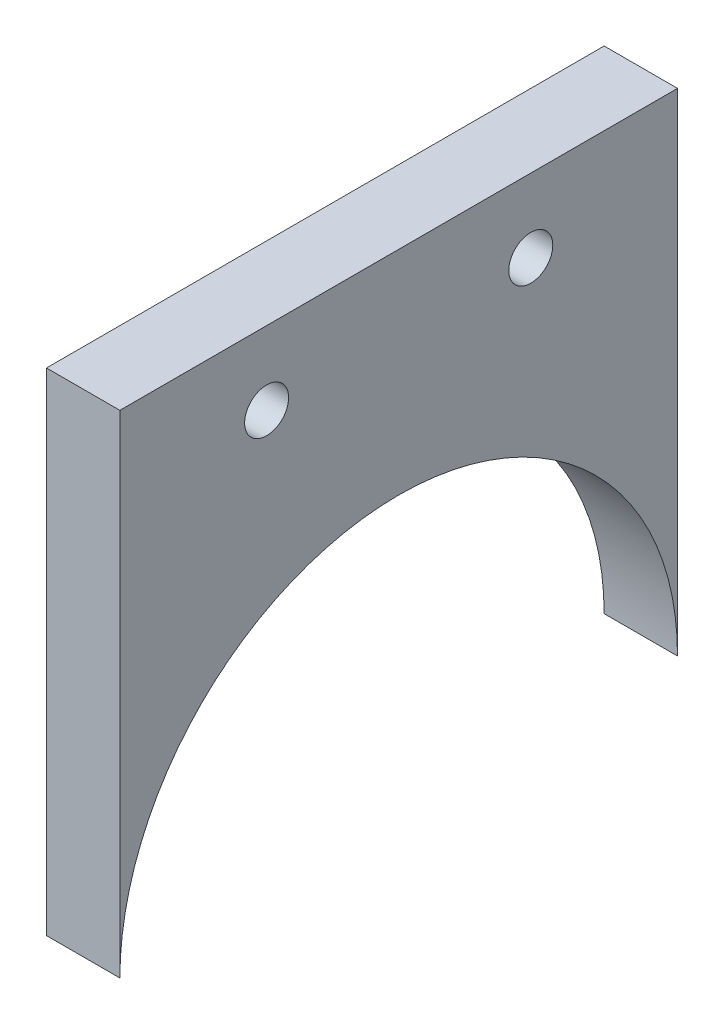
SolidWorks part; units mm, degrees
material "PMMA"
ref_plane "Front Plane" through (0, 0, 0) normal (0, 0, 1) x (1, 0, 0)
ref_plane "Top Plane" through (0, 0, 0) normal (0, 1, 0) x (1, 0, 0)
ref_plane "Right Plane" through (0, 0, 0) normal (1, 0, 0) x (0, 0, -1)
sketch "Schizzo1" plane through (0, 0, 0) normal (1, 0, 0) x (0, 0, -1)
  line L0 (19, 16.75) -> (-19, -16.75) construction
  line L1 (-19, 16.75) -> (19, 16.75)
  line L2 (-19, 16.75) -> (-19, -16.75)
  line L3 (-19, -16.75) -> (19, -16.75)
  line L4 (19, 16.75) -> (19, -16.75)
  point P4 (0, 0)
  dimension "D1" = 38
  dimension "D2" = 33.5
extrude "Estrusione-Estrusione1" add sketch "Schizzo1" along normal blind 5
sketch "Schizzo2" plane through (0, 0, 0) normal (1, 0, 0) x (0, 0, -1)
  line L0 (-19, -16.75) -> (19, -16.75) construction
  line L1 (-19, 16.75) -> (-19, -16.75) construction
  line L2 (19, 16.75) -> (-19, 16.75) construction
  line L3 (19, -16.75) -> (19, 16.75) construction
  line L4 (0, 16.75) -> (0, 2.25) construction
  circle A0 centre (0, -16.75) radius 19
  circle A1 centre (-9, 11.75) radius 1.5
  circle A2 centre (9, 11.75) radius 1.5
  dimension "D1" = 3
  dimension "D2" = 10
  dimension "D3" = 5
  dimension "D4" = 9
  dimension "D5" = 10
extrude "Taglio-Estrusione1" cut sketch "Schizzo2" along direction (1, 0, 0) on the side of the normal through all
equation "\"Thickness\"=5"
equation "\"D1@Estrusione-Estrusione1\"=\"Thickness\""
